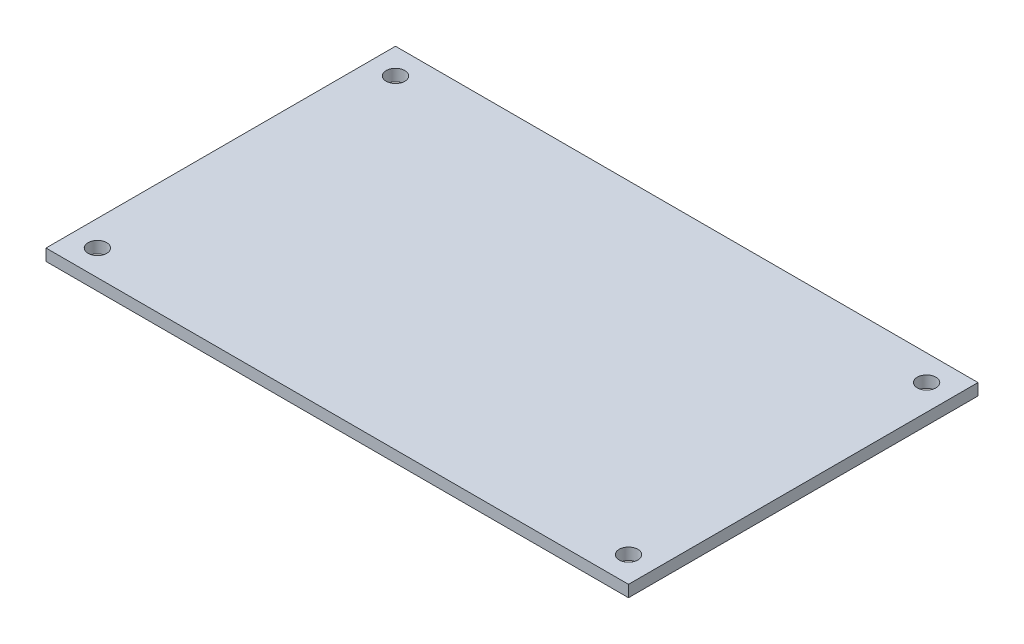
SolidWorks part; units mm, degrees
ref_plane "Спереди" through (0, 0, 0) normal (0, 0, 1) x (1, 0, 0)
ref_plane "Сверху" through (0, 0, 0) normal (0, 1, 0) x (1, 0, 0)
ref_plane "Справа" through (0, 0, 0) normal (1, 0, 0) x (0, 0, -1)
other "Configuration Table"
sketch "Эскиз1" plane through (0, 0, 0) normal (0, 1, 0) x (1, 0, 0)
  line L0 (-50, 30) -> (-45.5877, 25.5877) construction
  line L1 (50, -30) -> (-50, -30)
  line L2 (50, -30) -> (50, 30)
  line L3 (50, 30) -> (-50, 30)
  line L4 (-50, -30) -> (-50, 30)
  line L5 (50, -30) -> (-50, 30) construction
  line L6 (50, 30) -> (-50, -30) construction
  line L7 (0, 30) -> (0, -30) construction
  line L9 (-50, 0) -> (50, 0) construction
  circle A0 centre (-45.5877, 25.5877) radius 1.6
  circle A1 centre (45.5877, 25.5877) radius 1.6
  circle A2 centre (45.5877, -25.5877) radius 1.6
  circle A3 centre (-45.5877, -25.5877) radius 1.6
  point P0 (0, 0)
  dimension "D4" = 3.2
  dimension "D1" = 100
  dimension "D2" = 60
  dimension "D3" = 45
  dimension "D5" = 6.24
extrude "Бобышка-Вытянуть1" add sketch "Эскиз1" along normal blind 2
